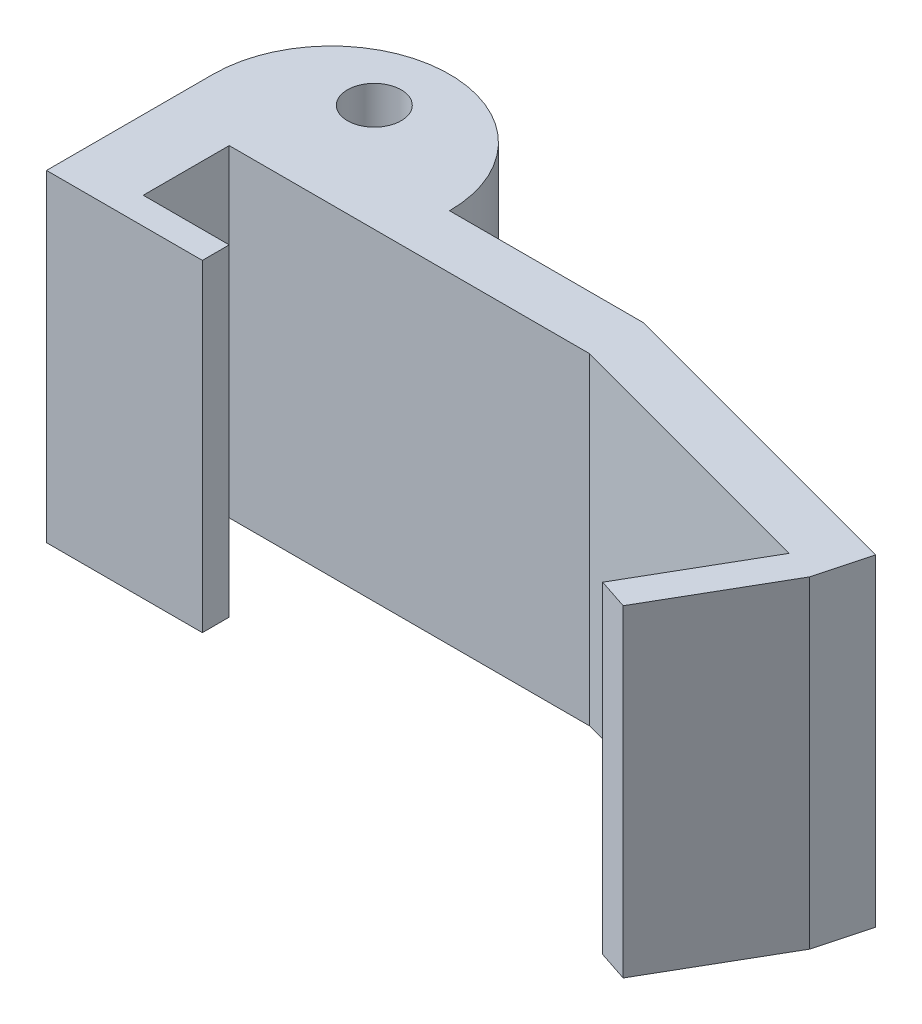
SolidWorks part; units mm, degrees
ref_plane "Front Plane" through (0, 0, 0) normal (0, 0, 1) x (1, 0, 0)
ref_plane "Top Plane" through (0, 0, 0) normal (0, 1, 0) x (1, 0, 0)
ref_plane "Right Plane" through (0, 0, 0) normal (1, 0, 0) x (0, 0, -1)
sketch "Sketch1" plane through (0, 0, 0) normal (0, 1, 0) x (1, 0, 0)
  line L0 (0, 0) -> (4.4, 0)
  line L1 (8, 0) -> (4.4, 0)
  line L2 (0, 0) -> (0, -1)
  line L3 (1.3, -1) -> (8, -1)
  line L4 (13.9101, -1.5836) -> (13.6513, -2.5495)
  line L5 (13.6513, -2.5495) -> (13.0815, -2.3616)
  line L6 (13.6513, -2.5495) -> (12.3812, -4.7495)
  line L7 (12.3812, -4.7495) -> (11.8114, -4.5616)
  line L8 (13.0815, -2.3616) -> (11.8114, -4.5616)
  line L9 (0, -1) -> (1.3, -1)
  line L10 (0, -1) -> (0, -3.1)
  line L11 (0, -3.1) -> (1.3, -3.1)
  line L12 (1.3, -1) -> (1.3, -3.1)
  line L13 (1.3, -3.1) -> (2.9, -3.1)
  line L14 (1.3, -3.1) -> (1.3, -2.6)
  line L15 (1.3, -2.6) -> (2.9, -2.6)
  line L16 (2.9, -3.1) -> (2.9, -2.6)
  line L17 (13.0815, -2.3616) -> (8, -1)
  line L18 (8, 0) -> (13.9101, -1.5836)
  arc A0 (0, 0) -> (4.4, 0) centre (2.2, 0) cw
  circle A1 centre (2, 1) radius 0.5
  dimension "D10" = 1
  dimension "D11" = 2.2
  dimension "D12" = 1.6
  dimension "D13" = 2
  dimension "D1" = 14
  dimension "D2" = 0.6
  dimension "D3" = 1
  dimension "D4" = 75
  dimension "D5" = 0.5
  dimension "D6" = 1.3
  dimension "D7" = 1.6
  dimension "D8" = 2.2
  dimension "D9" = 1
  dimension "D14" = 8
  dimension "D15" = 165
extrude "Boss-Extrude1" add sketch "Sketch1" along normal blind 6
